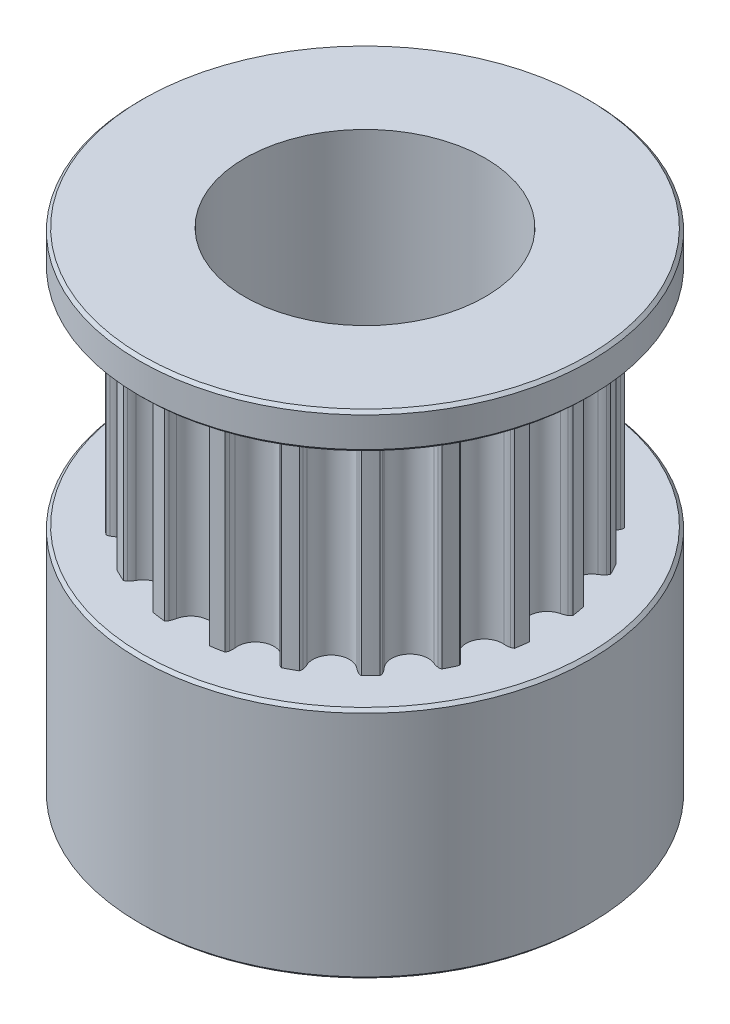
SolidWorks part; units mm, degrees
material "2024-T3"
ref_plane "Přední rovina" through (0, 0, 0) normal (0, 0, 1) x (1, 0, 0)
ref_plane "Horní rovina" through (0, 0, 0) normal (0, 1, 0) x (1, 0, 0)
ref_plane "Pravá rovina" through (0, 0, 0) normal (1, 0, 0) x (0, 0, -1)
sketch "Skica1" plane through (0, 0, 0) normal (0, 1, 0) x (1, 0, 0)
  circle A0 centre (0, 0) radius 4
  circle A1 centre (0, 0) radius 6.1087 construction
  circle A2 centre (0, 0) radius 6.4237 construction
  arc B0 (-5.7301, 1.0983) -> (-5.3872, 2.2403) centre (-5.6803, 1.7058) ccw
  arc B1 (-5.7301, 1.0983) -> (-5.922, 1.0859) centre (-5.7841, 0.4401) ccw
  arc B2 (-5.922, 1.0859) -> (-6.0197, 1.0387) centre (-5.8743, 0.8624) ccw
  arc B3 (-6.0197, 1.0387) -> (-6.0791, 0.6004) centre (0, 0) ccw
  arc B4 (-6.0791, 0.6004) -> (-5.9974, 0.5289) centre (-5.892, 0.7317) ccw
  arc B5 (-5.9974, 0.5289) -> (-5.8158, 0.466) centre (-5.6927, 1.1148) ccw
  arc B6 (-5.7891, -0.7262) -> (-5.8158, 0.466) centre (-5.9294, -0.133) ccw
  arc B7 (-5.7891, -0.7262) -> (-5.9677, -0.7972) centre (-5.637, -1.3689) ccw
  arc B8 (-5.9677, -0.7972) -> (-6.0461, -0.8723) centre (-5.8532, -0.9951) ccw
  arc B9 (-6.0461, -0.8723) -> (-5.9671, -1.3075) centre (0, 0) ccw
  arc B10 (-5.9671, -1.3075) -> (-5.8673, -1.3503) centre (-5.8297, -1.1248) ccw
  arc B11 (-5.8673, -1.3503) -> (-5.6751, -1.354) centre (-5.7586, -0.6989) ccw
  arc B12 (-5.2813, -2.4796) -> (-5.6751, -1.354) centre (-5.5981, -1.9587) ccw
  arc B13 (-5.2813, -2.4796) -> (-5.4293, -2.6023) centre (-4.9381, -3.0438) ccw
  arc B14 (-5.4293, -2.6023) -> (-5.4806, -2.698) centre (-5.2593, -2.7551) ccw
  arc B15 (-5.4806, -2.698) -> (-5.271, -3.0875) centre (0, 0) ccw
  arc B16 (-5.271, -3.0875) -> (-5.1629, -3.0973) centre (-5.1968, -2.8713) ccw
  arc B17 (-5.1629, -3.0973) -> (-4.979, -3.0415) centre (-5.2608, -2.4442) ccw
  arc B18 (-4.2566, -3.9902) -> (-4.979, -3.0415) centre (-4.7188, -3.5928) ccw
  arc B19 (-4.2566, -3.9902) -> (-4.3594, -4.1527) centre (-3.7559, -4.4208) ccw
  arc B20 (-4.3594, -4.1527) -> (-4.3786, -4.2595) centre (-4.1505, -4.2455) ccw
  arc B21 (-4.3786, -4.2595) -> (-4.059, -4.5652) centre (0, 0) ccw
  arc B22 (-4.059, -4.5652) -> (-3.9531, -4.5412) centre (-4.0552, -4.3366) ccw
  arc B23 (-3.9531, -4.5412) -> (-3.7954, -4.4312) centre (-4.248, -3.9503) ccw
  arc B24 (-2.8152, -5.1103) -> (-3.7954, -4.4312) centre (-3.3776, -4.8751) ccw
  arc B25 (-2.8152, -5.1103) -> (-2.8628, -5.2965) centre (-2.2059, -5.3651) ccw
  arc B26 (-2.8628, -5.2965) -> (-2.8481, -5.4041) centre (-2.6354, -5.3203) ccw
  arc B27 (-2.8481, -5.4041) -> (-2.4496, -5.596) centre (0, 0) ccw
  arc B28 (-2.4496, -5.596) -> (-2.3563, -5.5405) centre (-2.5166, -5.3775) ccw
  arc B29 (-2.3563, -5.5405) -> (-2.2403, -5.3872) centre (-2.8194, -5.0696) ccw
  arc B30 (-1.0983, -5.7301) -> (-2.2403, -5.3872) centre (-1.7058, -5.6803) ccw
  arc B31 (-1.0983, -5.7301) -> (-1.0859, -5.922) centre (-0.4401, -5.7841) ccw
  arc B32 (-1.0859, -5.922) -> (-1.0387, -6.0197) centre (-0.8624, -5.8743) ccw
  arc B33 (-1.0387, -6.0197) -> (-0.6004, -6.0791) centre (0, 0) ccw
  arc B34 (-0.6004, -6.0791) -> (-0.5289, -5.9974) centre (-0.7317, -5.892) ccw
  arc B35 (-0.5289, -5.9974) -> (-0.466, -5.8158) centre (-1.1148, -5.6927) ccw
  arc B36 (0.7262, -5.7891) -> (-0.466, -5.8158) centre (0.133, -5.9294) ccw
  arc B37 (0.7262, -5.7891) -> (0.7972, -5.9677) centre (1.3689, -5.637) ccw
  arc B38 (0.7972, -5.9677) -> (0.8723, -6.0461) centre (0.9951, -5.8532) ccw
  arc B39 (0.8723, -6.0461) -> (1.3075, -5.9671) centre (0, 0) ccw
  arc B40 (1.3075, -5.9671) -> (1.3503, -5.8673) centre (1.1248, -5.8297) ccw
  arc B41 (1.3503, -5.8673) -> (1.354, -5.6751) centre (0.6989, -5.7586) ccw
  arc B42 (2.4796, -5.2813) -> (1.354, -5.6751) centre (1.9587, -5.5981) ccw
  arc B43 (2.4796, -5.2813) -> (2.6023, -5.4293) centre (3.0438, -4.9381) ccw
  arc B44 (2.6023, -5.4293) -> (2.698, -5.4806) centre (2.7551, -5.2593) ccw
  arc B45 (2.698, -5.4806) -> (3.0875, -5.271) centre (0, 0) ccw
  arc B46 (3.0875, -5.271) -> (3.0973, -5.1629) centre (2.8713, -5.1968) ccw
  arc B47 (3.0973, -5.1629) -> (3.0415, -4.979) centre (2.4442, -5.2608) ccw
  arc B48 (3.9902, -4.2566) -> (3.0415, -4.979) centre (3.5928, -4.7188) ccw
  arc B49 (3.9902, -4.2566) -> (4.1527, -4.3594) centre (4.4208, -3.7559) ccw
  arc B50 (4.1527, -4.3594) -> (4.2595, -4.3786) centre (4.2455, -4.1505) ccw
  arc B51 (4.2595, -4.3786) -> (4.5652, -4.059) centre (0, 0) ccw
  arc B52 (4.5652, -4.059) -> (4.5412, -3.9531) centre (4.3366, -4.0552) ccw
  arc B53 (4.5412, -3.9531) -> (4.4312, -3.7954) centre (3.9503, -4.248) ccw
  arc B54 (5.1103, -2.8152) -> (4.4312, -3.7954) centre (4.8751, -3.3776) ccw
  arc B55 (5.1103, -2.8152) -> (5.2965, -2.8628) centre (5.3651, -2.2059) ccw
  arc B56 (5.2965, -2.8628) -> (5.4041, -2.8481) centre (5.3203, -2.6354) ccw
  arc B57 (5.4041, -2.8481) -> (5.596, -2.4496) centre (0, 0) ccw
  arc B58 (5.596, -2.4496) -> (5.5405, -2.3563) centre (5.3775, -2.5166) ccw
  arc B59 (5.5405, -2.3563) -> (5.3872, -2.2403) centre (5.0696, -2.8194) ccw
  arc B60 (5.7301, -1.0983) -> (5.3872, -2.2403) centre (5.6803, -1.7058) ccw
  arc B61 (5.7301, -1.0983) -> (5.922, -1.0859) centre (5.7841, -0.4401) ccw
  arc B62 (5.922, -1.0859) -> (6.0197, -1.0387) centre (5.8743, -0.8624) ccw
  arc B63 (6.0197, -1.0387) -> (6.0791, -0.6004) centre (0, 0) ccw
  arc B64 (6.0791, -0.6004) -> (5.9974, -0.5289) centre (5.892, -0.7317) ccw
  arc B65 (5.9974, -0.5289) -> (5.8158, -0.466) centre (5.6927, -1.1148) ccw
  arc B66 (5.7891, 0.7262) -> (5.8158, -0.466) centre (5.9294, 0.133) ccw
  arc B67 (5.7891, 0.7262) -> (5.9677, 0.7972) centre (5.637, 1.3689) ccw
  arc B68 (5.9677, 0.7972) -> (6.0461, 0.8723) centre (5.8532, 0.9951) ccw
  arc B69 (6.0461, 0.8723) -> (5.9671, 1.3075) centre (0, 0) ccw
  arc B70 (5.9671, 1.3075) -> (5.8673, 1.3503) centre (5.8297, 1.1248) ccw
  arc B71 (5.8673, 1.3503) -> (5.6751, 1.354) centre (5.7586, 0.6989) ccw
  arc B72 (5.2813, 2.4796) -> (5.6751, 1.354) centre (5.5981, 1.9587) ccw
  arc B73 (5.2813, 2.4796) -> (5.4293, 2.6023) centre (4.9381, 3.0438) ccw
  arc B74 (5.4293, 2.6023) -> (5.4806, 2.698) centre (5.2593, 2.7551) ccw
  arc B75 (5.4806, 2.698) -> (5.271, 3.0875) centre (0, 0) ccw
  arc B76 (5.271, 3.0875) -> (5.1629, 3.0973) centre (5.1968, 2.8713) ccw
  arc B77 (5.1629, 3.0973) -> (4.979, 3.0415) centre (5.2608, 2.4442) ccw
  arc B78 (4.2566, 3.9902) -> (4.979, 3.0415) centre (4.7188, 3.5928) ccw
  arc B79 (4.2566, 3.9902) -> (4.3594, 4.1527) centre (3.7559, 4.4208) ccw
  arc B80 (4.3594, 4.1527) -> (4.3786, 4.2595) centre (4.1505, 4.2455) ccw
  arc B81 (4.3786, 4.2595) -> (4.059, 4.5652) centre (0, 0) ccw
  arc B82 (4.059, 4.5652) -> (3.9531, 4.5412) centre (4.0552, 4.3366) ccw
  arc B83 (3.9531, 4.5412) -> (3.7954, 4.4312) centre (4.248, 3.9503) ccw
  arc B84 (2.8152, 5.1103) -> (3.7954, 4.4312) centre (3.3776, 4.8751) ccw
  arc B85 (2.8152, 5.1103) -> (2.8628, 5.2965) centre (2.2059, 5.3651) ccw
  arc B86 (2.8628, 5.2965) -> (2.8481, 5.4041) centre (2.6354, 5.3203) ccw
  arc B87 (2.8481, 5.4041) -> (2.4496, 5.596) centre (0, 0) ccw
  arc B88 (2.4496, 5.596) -> (2.3563, 5.5405) centre (2.5166, 5.3775) ccw
  arc B89 (2.3563, 5.5405) -> (2.2403, 5.3872) centre (2.8194, 5.0696) ccw
  arc B90 (1.0983, 5.7301) -> (2.2403, 5.3872) centre (1.7058, 5.6803) ccw
  arc B91 (1.0983, 5.7301) -> (1.0859, 5.922) centre (0.4401, 5.7841) ccw
  arc B92 (1.0859, 5.922) -> (1.0387, 6.0197) centre (0.8624, 5.8743) ccw
  arc B93 (1.0387, 6.0197) -> (0.6004, 6.0791) centre (0, 0) ccw
  arc B94 (0.6004, 6.0791) -> (0.5289, 5.9974) centre (0.7317, 5.892) ccw
  arc B95 (0.5289, 5.9974) -> (0.466, 5.8158) centre (1.1148, 5.6927) ccw
  arc B96 (-0.7262, 5.7891) -> (0.466, 5.8158) centre (-0.133, 5.9294) ccw
  arc B97 (-0.7262, 5.7891) -> (-0.7972, 5.9677) centre (-1.3689, 5.637) ccw
  arc B98 (-0.7972, 5.9677) -> (-0.8723, 6.0461) centre (-0.9951, 5.8532) ccw
  arc B99 (-0.8723, 6.0461) -> (-1.3075, 5.9671) centre (0, 0) ccw
  arc B100 (-1.3075, 5.9671) -> (-1.3503, 5.8673) centre (-1.1248, 5.8297) ccw
  arc B101 (-1.3503, 5.8673) -> (-1.354, 5.6751) centre (-0.6989, 5.7586) ccw
  arc B102 (-2.4796, 5.2813) -> (-1.354, 5.6751) centre (-1.9587, 5.5981) ccw
  arc B103 (-2.4796, 5.2813) -> (-2.6023, 5.4293) centre (-3.0438, 4.9381) ccw
  arc B104 (-2.6023, 5.4293) -> (-2.698, 5.4806) centre (-2.7551, 5.2593) ccw
  arc B105 (-2.698, 5.4806) -> (-3.0875, 5.271) centre (0, 0) ccw
  arc B106 (-3.0875, 5.271) -> (-3.0973, 5.1629) centre (-2.8713, 5.1968) ccw
  arc B107 (-3.0973, 5.1629) -> (-3.0415, 4.979) centre (-2.4442, 5.2608) ccw
  arc B108 (-3.9902, 4.2566) -> (-3.0415, 4.979) centre (-3.5928, 4.7188) ccw
  arc B109 (-3.9902, 4.2566) -> (-4.1527, 4.3594) centre (-4.4208, 3.7559) ccw
  arc B110 (-4.1527, 4.3594) -> (-4.2595, 4.3786) centre (-4.2455, 4.1505) ccw
  arc B111 (-4.2595, 4.3786) -> (-4.5652, 4.059) centre (0, 0) ccw
  arc B112 (-4.5652, 4.059) -> (-4.5412, 3.9531) centre (-4.3366, 4.0552) ccw
  arc B113 (-4.5412, 3.9531) -> (-4.4312, 3.7954) centre (-3.9503, 4.248) ccw
  arc B114 (-5.1103, 2.8152) -> (-4.4312, 3.7954) centre (-4.8751, 3.3776) ccw
  arc B115 (-5.1103, 2.8152) -> (-5.2965, 2.8628) centre (-5.3651, 2.2059) ccw
  arc B116 (-5.2965, 2.8628) -> (-5.4041, 2.8481) centre (-5.3203, 2.6354) ccw
  arc B117 (-5.4041, 2.8481) -> (-5.596, 2.4496) centre (0, 0) ccw
  arc B118 (-5.596, 2.4496) -> (-5.5405, 2.3563) centre (-5.3775, 2.5166) ccw
  arc B119 (-5.5405, 2.3563) -> (-5.3872, 2.2403) centre (-5.0696, 2.8194) ccw
  dimension "D1" = 8
  dimension "D2" = 0.315
sketch_block_instance "Blok1-1"
sketch_block "Blok1"
extrude "Přidat vysunutím1" add sketch "Skica1" along normal blind 7.4 from offset 7.8
sketch "Skica2" plane through (0, 7.8, 0) normal (0, -1, 0) x (1, 0, 0)
  circle A0 centre (0, 0) radius 4.5
  circle A1 centre (0, 0) radius 4 construction
  circle A2 centre (0, 0) radius 4
  dimension "D1" = 9
extrude "Přidat vysunutím2" add sketch "Skica2" along normal blind 7.8
sketch "Skica3" plane through (0, 15.2, 0) normal (0, 1, 0) x (1, 0, 0)
  circle A0 centre (0, 0) radius 3.5
  circle A1 centre (0, 0) radius 4 construction
  circle A2 centre (0, 0) radius 4
  dimension "D1" = 7
extrude "Přidat vysunutím3" add sketch "Skica3" along normal blind 1.2
sketch "Skica5" plane through (0, 16.4, 0) normal (0, 1, 0) x (1, 0, 0)
  circle A0 centre (0, 0) radius 7.5
  circle A1 centre (0, 0) radius 3.5 construction
  circle A4 centre (0, 0) radius 3.5
  dimension "D1" = 15
extrude "Přidat vysunutím4" add sketch "Skica5" against normal up to surface (1.2 mm away) separate body up to face at (0, 15.2, 0)
sketch "Skica6" plane through (0, 0, 0) normal (0, -1, 0) x (1, 0, 0)
  circle A0 centre (0, 0) radius 7.5
  circle A2 centre (0, 0) radius 4
  circle A3 centre (0, 0) radius 7.5 construction
  circle A5 centre (0, 0) radius 4 construction
extrude "Přidat vysunutím5" add sketch "Skica6" against normal up to surface (7.8 mm away) separate body up to face at (0, 7.8, 0)
chamfer "Zkosení1" distance 0.1 angle 45 2 edges at (0, 15.2, 7.5) (0, 16.4, 7.5)
chamfer "Zkosení3" distance 0.1 angle 45 2 edges at (0, 0, -7.5) (0, 7.8, 7.5)
combine bodies "Combine1" operation type add bodies to combine 102 104 103 105
sketch "Sketch1" plane through (0, 15.2, 0) normal (0, -1, 0) x (1, 0, 0)
  circle A1 centre (0, 0) radius 4
  circle A2 centre (0, 0) radius 4
  dimension "D1" = 0
extrude "Cut-Extrude1" cut sketch "Sketch1" against normal through all
